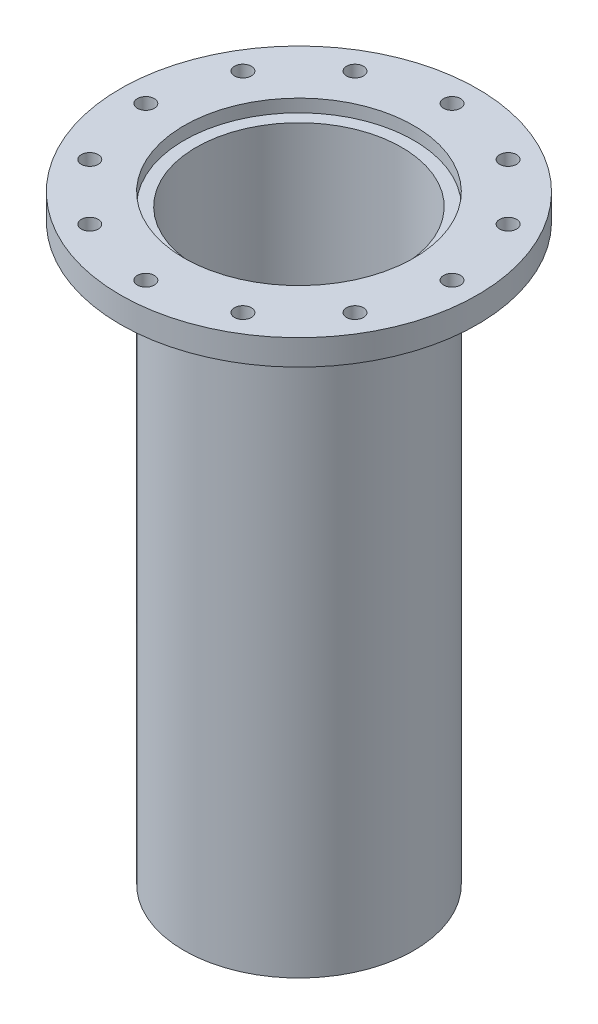
SolidWorks part; units mm, degrees
ref_plane "Front Plane" through (0, 0, 0) normal (0, 0, 1) x (1, 0, 0)
ref_plane "Top Plane" through (0, 0, 0) normal (0, 1, 0) x (1, 0, 0)
ref_plane "Right Plane" through (0, 0, 0) normal (1, 0, 0) x (0, 0, -1)
sketch "Sketch1" plane through (0, 0, 0) normal (0, 0, 1) x (1, 0, 0)
  line L0 (-57.15, 0) -> (-88.9, 0)
  line L1 (-88.9, 0) -> (-88.9, -12.7)
  line L2 (-88.9, -12.7) -> (-57.15, -12.7)
  line L3 (-57.15, -12.7) -> (-57.15, -298.45)
  line L4 (-57.15, -298.45) -> (-51.1302, -298.45)
  line L5 (-51.1302, -298.45) -> (-51.1302, -6.35)
  line L6 (-51.1302, -6.35) -> (-57.15, -6.35)
  line L7 (-57.15, -6.35) -> (-57.15, 0)
  line L8 (0, 0) -> (0, -50.8318) construction
  dimension "D1" = 51.1302
  dimension "D2" = 292.1
  dimension "D3" = 57.15
  dimension "D4" = 12.7
  dimension "D5" = 88.9
  dimension "D6" = 6.35
  dimension "D7" = 57.15
revolve "Revolve1" add sketch "Sketch1" angle 360 about L8
hole_wizard "5/16 Clearance Hole1" positions "Sketch2" profile "Sketch3" hole size "5/16" standard "ANSI Inch" end condition through all
sketch "Sketch2" plane through (0, 0, 0) normal (0, 1, 0) x (1, 0, 0)
  point P0 (-76.2, 0)
  dimension "D1" = 76.2
sketch "Sketch3" plane through (-76.2, 0, 0) normal (1, 0, 0) x (0, 0, 1)
  line L0 (0, 0) -> (0, 298.45)
  line L1 (0, 298.45) -> (4.2164, 298.45)
  line L2 (4.2164, 298.45) -> (4.2164, 0)
  line L5 (4.2164, 0) -> (0, 0)
  line L11 (0, -6.35) -> (0, 107.95) construction
  dimension "Thru Hole Dia." = 8.4328
  dimension "Thru Hole Depth" = 298.45
pattern_circular "CirPattern1" count 12 over 360 about axis through (0, 0, 0) along (0, 1, 0) of "5/16 Clearance Hole1"
